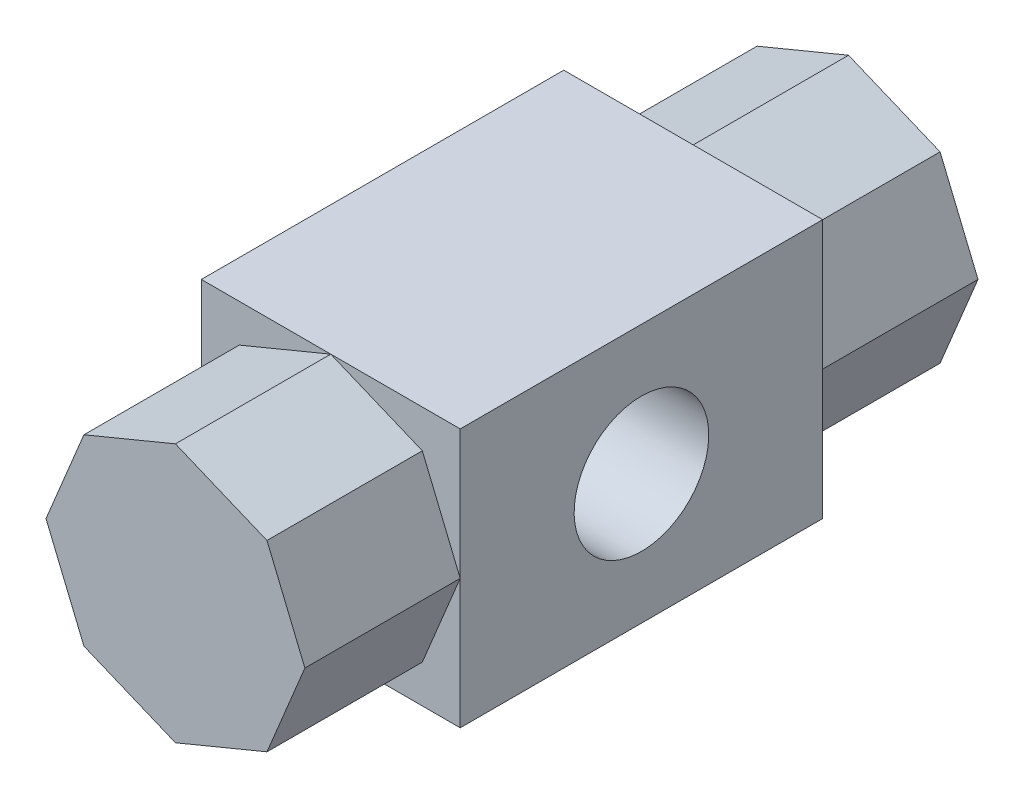
SolidWorks part; units mm, degrees
ref_plane "Front Plane" through (0, 0, 0) normal (0, 0, 1) x (1, 0, 0)
ref_plane "Top Plane" through (0, 0, 0) normal (0, 1, 0) x (1, 0, 0)
ref_plane "Right Plane" through (0, 0, 0) normal (1, 0, 0) x (0, 0, -1)
sketch "Sketch1" plane through (0, 0, 0) normal (0, 0, 1) x (1, 0, 0)
  line L1 (-25, 25) -> (25, 25)
  line L2 (-25, 25) -> (-25, -25)
  line L3 (-25, -25) -> (25, -25)
  line L4 (25, 25) -> (25, -25)
  line L5 (-25, 25) -> (25, -25) construction
  line L6 (-25, -25) -> (25, 25) construction
  point P0 (0, 0)
  dimension "D1" = 50
  dimension "D2" = 50
sketch "Sketch2" plane through (0, 0, 0) normal (0, 0, 1) x (1, 0, 0)
  line L0 (0, -25) -> (17.6777, -17.6777)
  line L1 (25, 0) -> (17.6777, 17.6777)
  line L2 (17.6777, 17.6777) -> (0, 25)
  line L3 (0, 25) -> (-17.6777, 17.6777)
  line L4 (-17.6777, 17.6777) -> (-25, 0)
  line L5 (-25, 0) -> (-17.6777, -17.6777)
  line L6 (-17.6777, -17.6777) -> (0, -25)
  line L7 (17.6777, -17.6777) -> (25, 0)
  circle A0 centre (0, 0) radius 23.097 construction
  dimension "D1" = 50
extrude "Boss-Extrude1" add sketch "Sketch2" along normal mid plane 130
extrude "Boss-Extrude2" add sketch "Sketch1" along normal mid plane 70
sketch "Sketch3" plane through (25, 0, 0) normal (1, 0, 0) x (0, 0, -1)
  circle A0 centre (0, 0) radius 13
extrude "Cut-Extrude1" cut sketch "Sketch3" against normal blind 70
